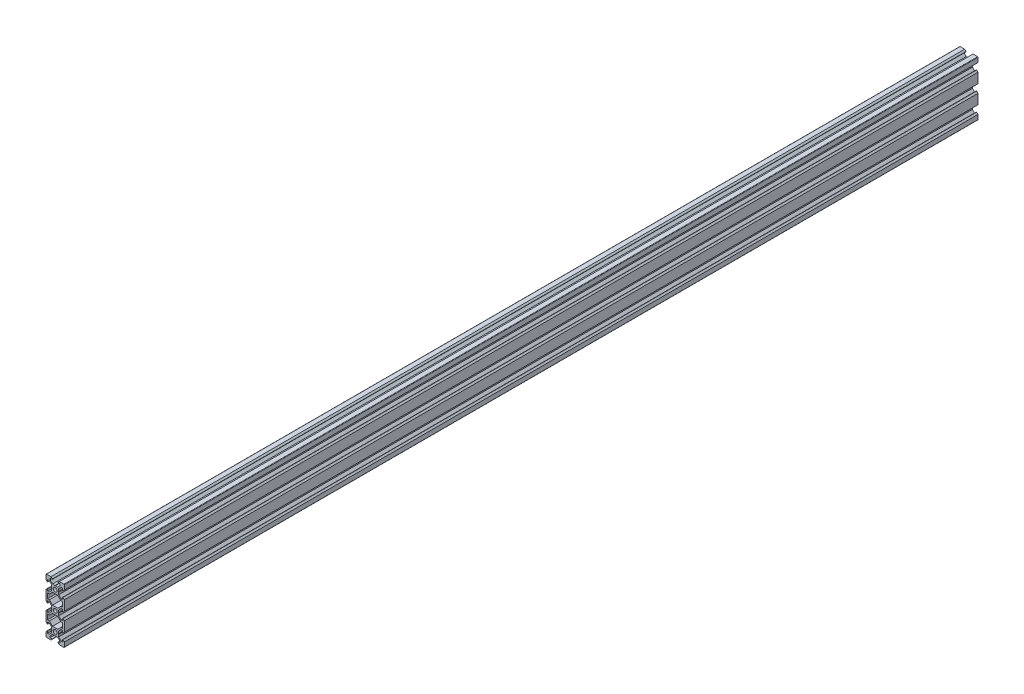
SolidWorks part; units mm, degrees
material "6061-T6 (SS)"
ref_plane "Front Plane" through (0, 0, 0) normal (0, 0, 1) x (1, 0, 0)
ref_plane "Top Plane" through (0, 0, 0) normal (0, 1, 0) x (1, 0, 0)
ref_plane "Right Plane" through (0, 0, 0) normal (1, 0, 0) x (0, 0, -1)
sketch "Sketch1" plane through (0, 0, 0) normal (0, 0, 1) x (1, 0, 0)
  line L0 (0, 0) -> (10, 0) construction
  line L1 (9.5, -30) -> (-9.5, -30)
  line L2 (10, -29.5) -> (10, 29.5)
  line L3 (9.5, 30) -> (-9.5, 30)
  line L4 (-10, -29.5) -> (-10, 29.5)
  line L5 (10, -30) -> (-10, 30) construction
  line L6 (10, 30) -> (-10, -30) construction
  circle A0 centre (0, 20) radius 2.1
  circle A1 centre (0, 0) radius 2.1
  circle A2 centre (0, -20) radius 2.1
  arc A3 (-9.5, -30) -> (-10, -29.5) centre (-9.5, -29.5) cw
  arc A4 (9.5, -30) -> (10, -29.5) centre (9.5, -29.5) ccw
  arc A5 (10, 29.5) -> (9.5, 30) centre (9.5, 29.5) ccw
  arc A6 (-9.5, 30) -> (-10, 29.5) centre (-9.5, 29.5) ccw
  point P0 (0, 0)
  line B0 (0, 20) -> (0, 30) construction
  line B1 (0, 23.69) -> (-0.21, 23.9)
  line B2 (-0.21, 23.9) -> (-2.8393, 23.9)
  line B3 (-2.8393, 23.9) -> (-5.5, 26.5607)
  line B4 (-5.5, 26.5607) -> (-5.5, 28.2)
  line B5 (-5.5, 28.2) -> (-3.125, 28.2)
  line B6 (-3.125, 28.2) -> (-3.125, 28.545)
  line B7 (-3.125, 28.545) -> (-4.58, 30)
  line B8 (-4.58, 30) -> (4.58, 30)
  line B9 (0, 20) -> (-5.9132, 25.9132) construction
  line B10 (3.125, 28.545) -> (4.58, 30)
  line B11 (3.125, 28.2) -> (3.125, 28.545)
  line B12 (5.5, 28.2) -> (3.125, 28.2)
  line B13 (5.5, 26.5607) -> (5.5, 28.2)
  line B14 (2.8393, 23.9) -> (5.5, 26.5607)
  line B15 (0.21, 23.9) -> (2.8393, 23.9)
  line B16 (0, 23.69) -> (0.21, 23.9)
  line B17 (0, 20) -> (-10, 20) construction
  line B18 (-3.69, 20) -> (-3.9, 19.79)
  line B19 (-3.9, 19.79) -> (-3.9, 17.1607)
  line B20 (-3.9, 17.1607) -> (-6.5607, 14.5)
  line B21 (-6.5607, 14.5) -> (-8.2, 14.5)
  line B22 (-8.2, 14.5) -> (-8.2, 16.875)
  line B23 (-8.2, 16.875) -> (-8.545, 16.875)
  line B24 (-8.545, 16.875) -> (-10, 15.42)
  line B25 (-10, 15.42) -> (-10, 24.58)
  line B26 (0, 20) -> (-5.9132, 14.0868) construction
  line B27 (-8.545, 23.125) -> (-10, 24.58)
  line B28 (-8.2, 23.125) -> (-8.545, 23.125)
  line B29 (-8.2, 25.5) -> (-8.2, 23.125)
  line B30 (-6.5607, 25.5) -> (-8.2, 25.5)
  line B31 (-3.9, 22.8393) -> (-6.5607, 25.5)
  line B32 (-3.9, 20.21) -> (-3.9, 22.8393)
  line B33 (-3.69, 20) -> (-3.9, 20.21)
  line B34 (0, 0) -> (-10, 0) construction
  line B35 (-3.69, 0) -> (-3.9, -0.21)
  line B36 (-3.9, -0.21) -> (-3.9, -2.8393)
  line B37 (-3.9, -2.8393) -> (-6.5607, -5.5)
  line B38 (-6.5607, -5.5) -> (-8.2, -5.5)
  line B39 (-8.2, -5.5) -> (-8.2, -3.125)
  line B40 (-8.2, -3.125) -> (-8.545, -3.125)
  line B41 (-8.545, -3.125) -> (-10, -4.58)
  line B42 (-10, -4.58) -> (-10, 4.58)
  line B43 (0, 0) -> (-5.9132, -5.9132) construction
  line B44 (-8.545, 3.125) -> (-10, 4.58)
  line B45 (-8.2, 3.125) -> (-8.545, 3.125)
  line B46 (-8.2, 5.5) -> (-8.2, 3.125)
  line B47 (-6.5607, 5.5) -> (-8.2, 5.5)
  line B48 (-3.9, 2.8393) -> (-6.5607, 5.5)
  line B49 (-3.9, 0.21) -> (-3.9, 2.8393)
  line B50 (-3.69, 0) -> (-3.9, 0.21)
  line B51 (0, -20) -> (-10, -20) construction
  line B52 (-3.69, -20) -> (-3.9, -20.21)
  line B53 (-3.9, -20.21) -> (-3.9, -22.8393)
  line B54 (-3.9, -22.8393) -> (-6.5607, -25.5)
  line B55 (-6.5607, -25.5) -> (-8.2, -25.5)
  line B56 (-8.2, -25.5) -> (-8.2, -23.125)
  line B57 (-8.2, -23.125) -> (-8.545, -23.125)
  line B58 (-8.545, -23.125) -> (-10, -24.58)
  line B59 (-10, -24.58) -> (-10, -15.42)
  line B60 (0, -20) -> (-5.9132, -25.9132) construction
  line B61 (-8.545, -16.875) -> (-10, -15.42)
  line B62 (-8.2, -16.875) -> (-8.545, -16.875)
  line B63 (-8.2, -14.5) -> (-8.2, -16.875)
  line B64 (-6.5607, -14.5) -> (-8.2, -14.5)
  line B65 (-3.9, -17.1607) -> (-6.5607, -14.5)
  line B66 (-3.9, -19.79) -> (-3.9, -17.1607)
  line B67 (-3.69, -20) -> (-3.9, -19.79)
  line B68 (0, -20) -> (0, -30) construction
  line B69 (0, -23.69) -> (0.21, -23.9)
  line B70 (0.21, -23.9) -> (2.8393, -23.9)
  line B71 (2.8393, -23.9) -> (5.5, -26.5607)
  line B72 (5.5, -26.5607) -> (5.5, -28.2)
  line B73 (5.5, -28.2) -> (3.125, -28.2)
  line B74 (3.125, -28.2) -> (3.125, -28.545)
  line B75 (3.125, -28.545) -> (4.58, -30)
  line B76 (4.58, -30) -> (-4.58, -30)
  line B77 (0, -20) -> (5.9132, -25.9132) construction
  line B78 (-3.125, -28.545) -> (-4.58, -30)
  line B79 (-3.125, -28.2) -> (-3.125, -28.545)
  line B80 (-5.5, -28.2) -> (-3.125, -28.2)
  line B81 (-5.5, -26.5607) -> (-5.5, -28.2)
  line B82 (-2.8393, -23.9) -> (-5.5, -26.5607)
  line B83 (-0.21, -23.9) -> (-2.8393, -23.9)
  line B84 (0, -23.69) -> (-0.21, -23.9)
  line B85 (0, -20) -> (10, -20) construction
  line B86 (3.69, -20) -> (3.9, -19.79)
  line B87 (3.9, -19.79) -> (3.9, -17.1607)
  line B88 (3.9, -17.1607) -> (6.5607, -14.5)
  line B89 (6.5607, -14.5) -> (8.2, -14.5)
  line B90 (8.2, -14.5) -> (8.2, -16.875)
  line B91 (8.2, -16.875) -> (8.545, -16.875)
  line B92 (8.545, -16.875) -> (10, -15.42)
  line B93 (10, -15.42) -> (10, -24.58)
  line B94 (0, -20) -> (5.9132, -14.0868) construction
  line B95 (8.545, -23.125) -> (10, -24.58)
  line B96 (8.2, -23.125) -> (8.545, -23.125)
  line B97 (8.2, -25.5) -> (8.2, -23.125)
  line B98 (6.5607, -25.5) -> (8.2, -25.5)
  line B99 (3.9, -22.8393) -> (6.5607, -25.5)
  line B100 (3.9, -20.21) -> (3.9, -22.8393)
  line B101 (3.69, -20) -> (3.9, -20.21)
  line B102 (0, 0) -> (10, 0) construction
  line B103 (3.69, 0) -> (3.9, 0.21)
  line B104 (3.9, 0.21) -> (3.9, 2.8393)
  line B105 (3.9, 2.8393) -> (6.5607, 5.5)
  line B106 (6.5607, 5.5) -> (8.2, 5.5)
  line B107 (8.2, 5.5) -> (8.2, 3.125)
  line B108 (8.2, 3.125) -> (8.545, 3.125)
  line B109 (8.545, 3.125) -> (10, 4.58)
  line B110 (10, 4.58) -> (10, -4.58)
  line B111 (0, 0) -> (5.9132, 5.9132) construction
  line B112 (8.545, -3.125) -> (10, -4.58)
  line B113 (8.2, -3.125) -> (8.545, -3.125)
  line B114 (8.2, -5.5) -> (8.2, -3.125)
  line B115 (6.5607, -5.5) -> (8.2, -5.5)
  line B116 (3.9, -2.8393) -> (6.5607, -5.5)
  line B117 (3.9, -0.21) -> (3.9, -2.8393)
  line B118 (3.69, 0) -> (3.9, -0.21)
  line B119 (0, 20) -> (10, 20) construction
  line B120 (3.69, 20) -> (3.9, 20.21)
  line B121 (3.9, 20.21) -> (3.9, 22.8393)
  line B122 (3.9, 22.8393) -> (6.5607, 25.5)
  line B123 (6.5607, 25.5) -> (8.2, 25.5)
  line B124 (8.2, 25.5) -> (8.2, 23.125)
  line B125 (8.2, 23.125) -> (8.545, 23.125)
  line B126 (8.545, 23.125) -> (10, 24.58)
  line B127 (10, 24.58) -> (10, 15.42)
  line B128 (0, 20) -> (5.9132, 25.9132) construction
  line B129 (8.545, 16.875) -> (10, 15.42)
  line B130 (8.2, 16.875) -> (8.545, 16.875)
  line B131 (8.2, 14.5) -> (8.2, 16.875)
  line B132 (6.5607, 14.5) -> (8.2, 14.5)
  line B133 (3.9, 17.1607) -> (6.5607, 14.5)
  line B134 (3.9, 19.79) -> (3.9, 17.1607)
  line B135 (3.69, 20) -> (3.9, 19.79)
  line B136 (-8.2, 7.3) -> (-8.2, 12.7)
  line B137 (-8.2, 12.7) -> (-6.2393, 12.7)
  line B138 (-6.2393, 12.7) -> (-2.8393, 16.1)
  line B139 (-2.8393, 16.1) -> (2.8393, 16.1)
  line B140 (0, 16.1) -> (0, 10) construction
  line B141 (0, 10) -> (-8.2, 10) construction
  line B142 (6.2393, 12.7) -> (2.8393, 16.1)
  line B143 (8.2, 12.7) -> (6.2393, 12.7)
  line B144 (8.2, 7.3) -> (8.2, 12.7)
  line B145 (8.2, 7.3) -> (6.2393, 7.3)
  line B146 (6.2393, 7.3) -> (2.8393, 3.9)
  line B147 (-2.8393, 3.9) -> (2.8393, 3.9)
  line B148 (-6.2393, 7.3) -> (-2.8393, 3.9)
  line B149 (-8.2, 7.3) -> (-6.2393, 7.3)
  line B150 (0, 16.1) -> (0, 20) construction
  line B151 (0, 20) -> (-5.0927, 14.9073) construction
  line B152 (-8.2, -12.7) -> (-8.2, -7.3)
  line B153 (-8.2, -7.3) -> (-6.2393, -7.3)
  line B154 (-6.2393, -7.3) -> (-2.8393, -3.9)
  line B155 (-2.8393, -3.9) -> (2.8393, -3.9)
  line B156 (0, -3.9) -> (0, -10) construction
  line B157 (0, -10) -> (-8.2, -10) construction
  line B158 (6.2393, -7.3) -> (2.8393, -3.9)
  line B159 (8.2, -7.3) -> (6.2393, -7.3)
  line B160 (8.2, -12.7) -> (8.2, -7.3)
  line B161 (8.2, -12.7) -> (6.2393, -12.7)
  line B162 (6.2393, -12.7) -> (2.8393, -16.1)
  line B163 (-2.8393, -16.1) -> (2.8393, -16.1)
  line B164 (-6.2393, -12.7) -> (-2.8393, -16.1)
  line B165 (-8.2, -12.7) -> (-6.2393, -12.7)
  line B166 (0, -3.9) -> (0, 0) construction
  line B167 (0, 0) -> (-5.0927, -5.0927) construction
  dimension "D3" = 4.2
  dimension "D5" = 0.5
  dimension "D1" = 20
  dimension "D2" = 60
  dimension "D4" = 40
sketch_block_instance "V Slot 1-4"
sketch_block "V Slot 1" parameters "D1"=10, "D2"=11, "D3"=4.3, "D4"=1.8, "D5"=0.21, "D6"=45, "D7"=9.16, "D8"=1.5, "D9"=6.25
sketch_block_instance "V Slot 1-5"
sketch_block_instance "V Slot 1-6"
sketch_block_instance "V Slot 1-7"
sketch_block_instance "V Slot 1-8"
sketch_block_instance "V Slot 1-9"
sketch_block_instance "V Slot 1-10"
sketch_block_instance "V Slot 1-11"
sketch_block_instance "Center Cutout 1-1"
sketch_block "Center Cutout 1" parameters "D1"=5.4, "D2"=12.2, "D3"=8.2, "D4"=45, "D5"=10, "D6"=1.5
sketch_block_instance "Center Cutout 1-2"
extrude "Boss-Extrude1" add sketch "Sketch1" along normal blind 1000 contours B135 B120 B121 B122 B123 B124 B125 B126 L2 A5 L3 B10 B11 B12 B13 B14 B15 B16 B1 B2 B3 B4 B5 B6 B7 A6 L4 B27 B28 B29 B30 B31 B32 B33 B18 B19 B20 B21 B22 B23 B24 B44 B45 B46 B47 B48 B49 B50 B35
